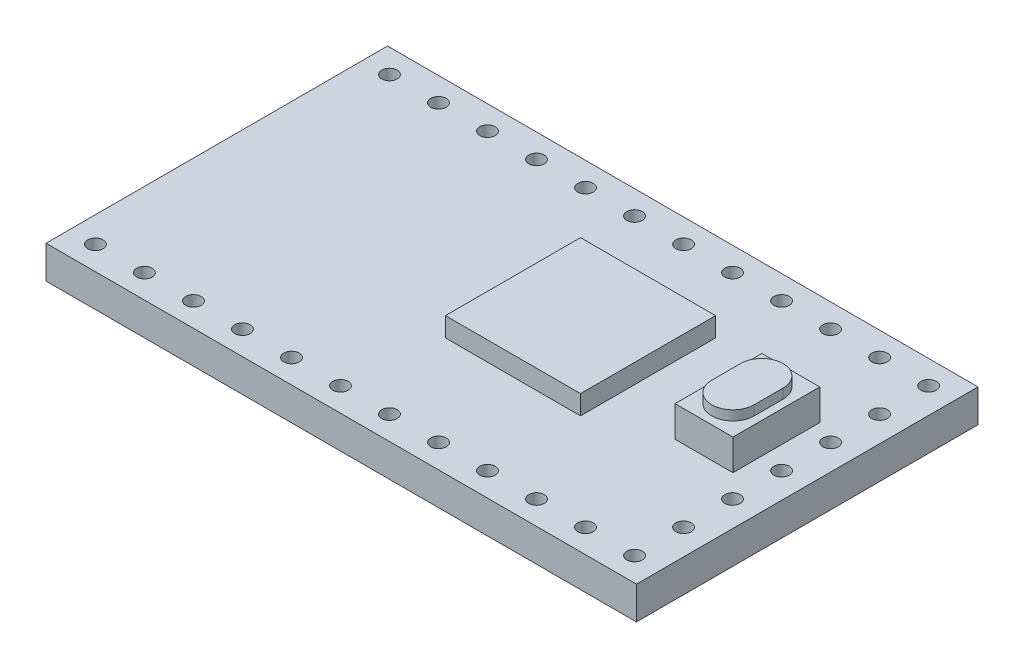
SolidWorks part; units mm, degrees
material "Acier non allié"
ref_plane "Plan de face" through (0, 0, 0) normal (0, 0, 1) x (1, 0, 0)
ref_plane "Plan de dessus" through (0, 0, 0) normal (0, 1, 0) x (1, 0, 0)
ref_plane "Plan de droite" through (0, 0, 0) normal (1, 0, 0) x (0, 0, -1)
sketch "Esquisse1" plane through (0, 0, 0) normal (0, 1, 0) x (1, 0, 0)
  line L1 (-15.3, 8.85) -> (15.3, 8.85)
  line L2 (-15.3, 8.85) -> (-15.3, -8.85)
  line L3 (-15.3, -8.85) -> (15.3, -8.85)
  line L4 (15.3, 8.85) -> (15.3, -8.85)
  line L5 (-15.3, 8.85) -> (15.3, -8.85) construction
  line L6 (-15.3, -8.85) -> (15.3, 8.85) construction
  point P0 (0, 0)
  dimension "D1" = 30.6
  dimension "D2" = 17.7
extrude "Boss.-Extru.1" add sketch "Esquisse1" along normal blind 1.7
sketch "Esquisse2" plane through (0, 1.7, 0) normal (0, 1, 0) x (1, 0, 0)
  line L0 (15.3, -8.85) -> (15.3, 8.85) construction
  line L1 (-0.7, 4.25) -> (6.3, 4.25)
  line L2 (-0.7, 4.25) -> (-0.7, -2.75)
  line L3 (-0.7, -2.75) -> (6.3, -2.75)
  line L4 (6.3, 4.25) -> (6.3, -2.75)
  line L5 (-0.7, 4.25) -> (6.3, -2.75) construction
  line L6 (-0.7, -2.75) -> (6.3, 4.25) construction
  line L7 (15.3, 8.85) -> (-15.3, 8.85) construction
  point P0 (2.8, 0.75)
  dimension "D1" = 7
  dimension "D2" = 7
  dimension "D3" = 9
  dimension "D4" = 4.6
extrude "Boss.-Extru.2" add sketch "Esquisse2" along normal blind 1
sketch "Esquisse3" plane through (0, 0, 0) normal (0, -1, 0) x (1, 0, 0)
  line L0 (-13.97, -7.62) -> (13.97, -7.62) construction
  line L1 (13.97, -7.62) -> (13.97, 7.62) construction
  line L2 (13.97, 7.62) -> (-13.97, 7.62) construction
  line L3 (15.3, 8.85) -> (15.3, -8.85) construction
  line L4 (-15.3, 8.85) -> (15.3, 8.85) construction
  line L5 (15.3, -8.85) -> (-15.3, -8.85) construction
  line L6 (-15.3, -8.85) -> (-15.3, 8.85) construction
  line L7 (-13.97, 7.62) -> (-13.97, -7.62) construction
  line L8 (-13.97, -7.62) -> (-11.43, -7.62) construction
  line L15 (13.97, -2.54) -> (13.97, 12.7) construction
  line L16 (13.97, 0) -> (13.97, 15.24) construction
  line L17 (13.97, 2.54) -> (13.97, 17.78) construction
  line L18 (13.97, 5.08) -> (13.97, 20.32) construction
  line L19 (13.97, 7.62) -> (13.97, 22.86) construction
  line L20 (13.97, -5.08) -> (13.97, 10.16) construction
  line L26 (8.89, 7.62) -> (-19.05, 7.62) construction
  line L27 (6.35, 7.62) -> (-21.59, 7.62) construction
  line L28 (3.81, 7.62) -> (-24.13, 7.62) construction
  line L29 (1.27, 7.62) -> (-26.67, 7.62) construction
  line L30 (-1.27, 7.62) -> (-29.21, 7.62) construction
  line L31 (-3.81, 7.62) -> (-31.75, 7.62) construction
  line L32 (-6.35, 7.62) -> (-34.29, 7.62) construction
  line L33 (-8.89, 7.62) -> (-36.83, 7.62) construction
  line L34 (-11.43, 7.62) -> (-39.37, 7.62) construction
  line L35 (-13.97, 7.62) -> (-41.91, 7.62) construction
  line L36 (11.43, 7.62) -> (-16.51, 7.62) construction
  circle A0 centre (-13.97, -7.62) radius 0.4
  circle A1 centre (-11.43, -7.62) radius 0.4
  circle A2 centre (-8.89, -7.62) radius 0.4
  circle A3 centre (-6.35, -7.62) radius 0.4
  circle A4 centre (-3.81, -7.62) radius 0.4
  circle A5 centre (-1.27, -7.62) radius 0.4
  circle A6 centre (1.27, -7.62) radius 0.4
  circle A7 centre (3.81, -7.62) radius 0.4
  circle A8 centre (6.35, -7.62) radius 0.4
  circle A9 centre (8.89, -7.62) radius 0.4
  circle A10 centre (11.43, -7.62) radius 0.4
  circle A11 centre (13.97, -7.62) radius 0.4
  circle A12 centre (13.97, -5.08) radius 0.4
  circle A13 centre (13.97, -2.54) radius 0.4
  circle A14 centre (13.97, 0) radius 0.4
  circle A15 centre (13.97, 2.54) radius 0.4
  circle A16 centre (13.97, 5.08) radius 0.4
  circle A17 centre (13.97, 7.62) radius 0.4
  circle A18 centre (11.43, 7.62) radius 0.4
  circle A19 centre (8.89, 7.62) radius 0.4
  circle A20 centre (6.35, 7.62) radius 0.4
  circle A21 centre (3.81, 7.62) radius 0.4
  circle A22 centre (1.27, 7.62) radius 0.4
  circle A23 centre (-1.27, 7.62) radius 0.4
  circle A24 centre (-3.81, 7.62) radius 0.4
  circle A25 centre (-6.35, 7.62) radius 0.4
  circle A26 centre (-8.89, 7.62) radius 0.4
  circle A27 centre (-11.43, 7.62) radius 0.4
  circle A28 centre (-13.97, 7.62) radius 0.4
  dimension "D5" = 0.8
  dimension "D1" = 1.33
  dimension "D2" = 1.23
  dimension "D3" = 1.33
  dimension "D4" = 1.23
  dimension "D7" = 2.54
  dimension "D8" = 15.24
  dimension "D6" = 12
  dimension "D9" = 7
  dimension "D10" = 12
extrude "Enlèv. mat.-Extru.1" cut sketch "Esquisse3" against normal through all
sketch "Esquisse4" plane through (0, 1.7, 0) normal (0, 1, 0) x (1, 0, 0)
  line L0 (15.3, -8.85) -> (15.3, 8.85) construction
  line L1 (9.8, 3.15) -> (12.8, 3.15)
  line L2 (9.8, 3.15) -> (9.8, -1.35)
  line L3 (9.8, -1.35) -> (12.8, -1.35)
  line L4 (12.8, 3.15) -> (12.8, -1.35)
  line L5 (9.8, 3.15) -> (12.8, -1.35) construction
  line L6 (9.8, -1.35) -> (12.8, 3.15) construction
  line L7 (15.3, 8.85) -> (-15.3, 8.85) construction
  point P0 (11.3, 0.9)
  dimension "D1" = 2.5
  dimension "D2" = 4.5
  dimension "D3" = 3
  dimension "D4" = 10.2
extrude "Boss.-Extru.3" add sketch "Esquisse4" along normal blind 1.6
sketch "Esquisse5" plane through (0, 3.3, 0) normal (0, 1, 0) x (1, 0, 0)
  line L0 (12.8, 3.15) -> (9.8, -1.35) construction
  line L1 (11.3, 1.65) -> (11.3, 0.15) construction
  line L2 (12.4, 1.65) -> (12.4, 0.15)
  line L3 (10.2, 1.65) -> (10.2, 0.15)
  line L4 (12.8, -1.35) -> (12.8, 3.15) construction
  line L5 (12.8, 3.15) -> (9.8, 3.15) construction
  arc A0 (12.4, 1.65) -> (10.2, 1.65) centre (11.3, 1.65) ccw
  arc A1 (10.2, 0.15) -> (12.4, 0.15) centre (11.3, 0.15) ccw
  point P6 (11.3, 0.9)
  dimension "D2" = 0.4
  dimension "D1" = 0.4
extrude "Boss.-Extru.4" add sketch "Esquisse5" along normal blind 0.5
